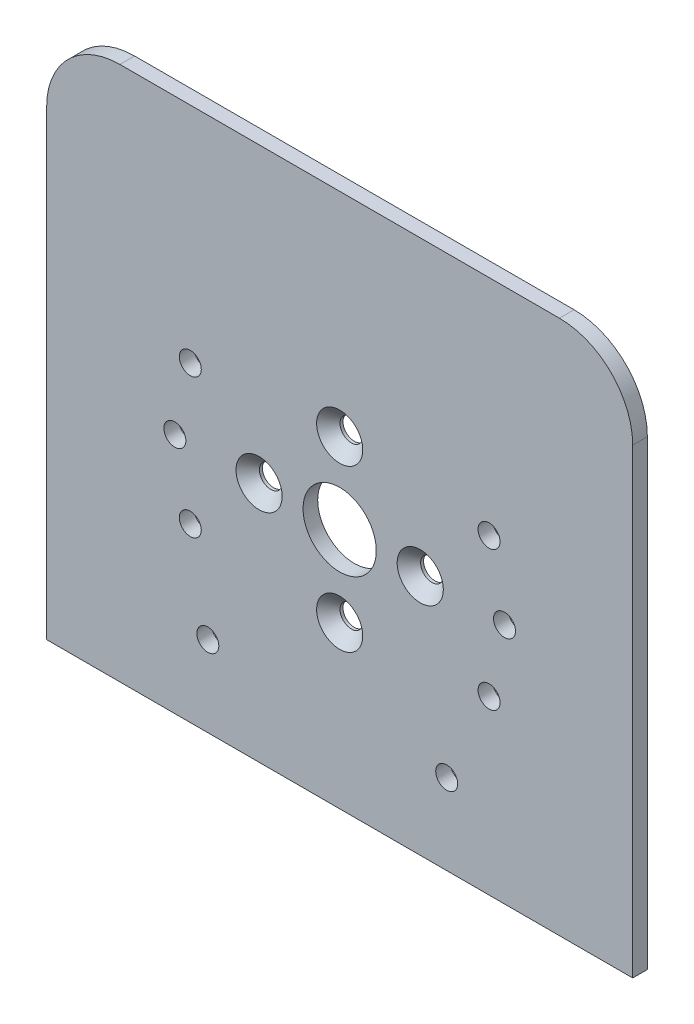
SolidWorks part; units mm, degrees
ref_plane "前视基准面" through (0, 0, 0) normal (0, 0, 1) x (1, 0, 0)
ref_plane "上视基准面" through (0, 0, 0) normal (0, 1, 0) x (1, 0, 0)
ref_plane "右视基准面" through (0, 0, 0) normal (1, 0, 0) x (0, 0, -1)
sketch "草图1" plane through (0, 0, -1.3) normal (0, 0, -1) x (-1, 0, 0)
  line L0 (52.9761, 0) -> (-56.7794, 0) construction
  line L1 (0, 22.1223) -> (0, -22.869) construction
  line L3 (40, 40) -> (-40, 40)
  line L4 (40, 40) -> (40, -33)
  line L5 (40, -33) -> (-40, -33)
  line L6 (-40, 40) -> (-40, -33)
  circle A0 centre (0, 0) radius 5 construction
  circle A1 centre (0, 0) radius 5
  dimension "D1" = 40
  dimension "D2" = 80
  dimension "D3" = 33
extrude "凸台-拉伸1" add sketch "草图1" along normal blind 2
hole_wizard "打孔尺寸(%根据十字)槽沉头自攻螺钉的类型1" positions "草图2" profile "草图3" countersink size "ST2.9" standard "GB"
sketch "草图2" plane through (0, 0, -1.3) normal (0, 0, 1) x (1, 0, 0)
  point P0 (11, 0)
  dimension "D1" = 11
sketch "草图3" plane through (11, 0, -1.3) normal (1, 0, 0) x (0, -1, 0)
  line L0 (0, 0) -> (0, 5.4313)
  line L1 (0, 5.4313) -> (1.55, 4.5)
  line L2 (1.55, 4.5) -> (1.55, 1.6)
  line L3 (1.55, 1.6) -> (3.15, 0)
  line L5 (3.15, 0) -> (0, 0)
  line L6 (-1.55, 1.6) -> (-3.15, 0) construction
  line L10 (0, 5.4313) -> (-1.55, 4.5) construction
  line L11 (0, -6.35) -> (0, 107.95) construction
  dimension "孔直径" = 3.1
  dimension "孔深度" = 4.5
  dimension "近端锥形沉头孔直径" = 6.3
  dimension "近端锥形沉头孔角度" = 90
  dimension "导头角度" = 118
pattern_circular "阵列(圆周)1" count 4 over 360 about axis through (0, 0, 0) along (0, 0, 1) of "打孔尺寸(%根据十字)槽沉头自攻螺钉的类型1"
fillet "圆角1" radius 10 2 edges at (40, 40, -2.3) (-40, 40, -2.3)
hole_wizard "大小mm Transitional 暗销孔1" positions "草图4" profile "草图5" hole size "Ø3.0" standard "GB" end condition through all
sketch "草图4" plane through (0, 0, -3.3) normal (0, 0, -1) x (-1, 0, 0)
  line L0 (0, 0) -> (0, -28.9908) construction
  line L2 (-15.7033, 0) -> (18.821, 0) construction
  point P0 (-14.6094, -22)
  point P2 (18, -22)
  dimension "D1" = 22
  dimension "D2" = 14.6094
  dimension "D3" = 18
  dimension "D4" = 22
sketch "草图5" plane through (14.6094, -22, -3.3) normal (1, 0, 0) x (0, 1, 0)
  line L0 (0, 0) -> (0, 2)
  line L1 (0, 2) -> (1.5, 2)
  line L2 (1.5, 2) -> (1.5, 0)
  line L5 (1.5, 0) -> (0, 0)
  line L11 (0, -6.35) -> (0, 107.95) construction
  dimension "通孔孔直径" = 3
  dimension "通孔孔深度" = 2
hole_wizard "大小mm Transitional 暗销孔2" positions "草图8" profile "草图7" hole size "Ø3.0" standard "GB" end condition through all
sketch "草图8" plane through (0, 0, -1.3) normal (0, 0, 1) x (1, 0, 0)
  line L0 (0, -7.2997) -> (0, 28.1232) construction
  line L2 (-29.4546, 0) -> (28.4437, 0) construction
  line L4 (0, 0) -> (-20.3919, 9.5089) construction
  arc A0 (-18.7049, 12.505) -> (-15.5586, -16.2536) centre (0, 0) ccw construction
  point P0 (-20.3919, -9.5089)
  point P2 (-22.5, 0)
  point P4 (-20.3919, 9.5089)
  point P11 (20.3919, -9.5089)
  point P12 (22.5, 0)
  point P13 (20.3919, 9.5089)
  dimension "D1" = 22.5
  dimension "D2" = 25
sketch "草图7" plane through (-20.3919, -9.5089, -1.3) normal (1, 0, 0) x (0, -1, 0)
  line L0 (0, 0) -> (0, 2)
  line L1 (0, 2) -> (1.5, 2)
  line L2 (1.5, 2) -> (1.5, 0)
  line L5 (1.5, 0) -> (0, 0)
  line L11 (0, -6.35) -> (0, 107.95) construction
  dimension "通孔孔直径" = 3
  dimension "通孔孔深度" = 2
